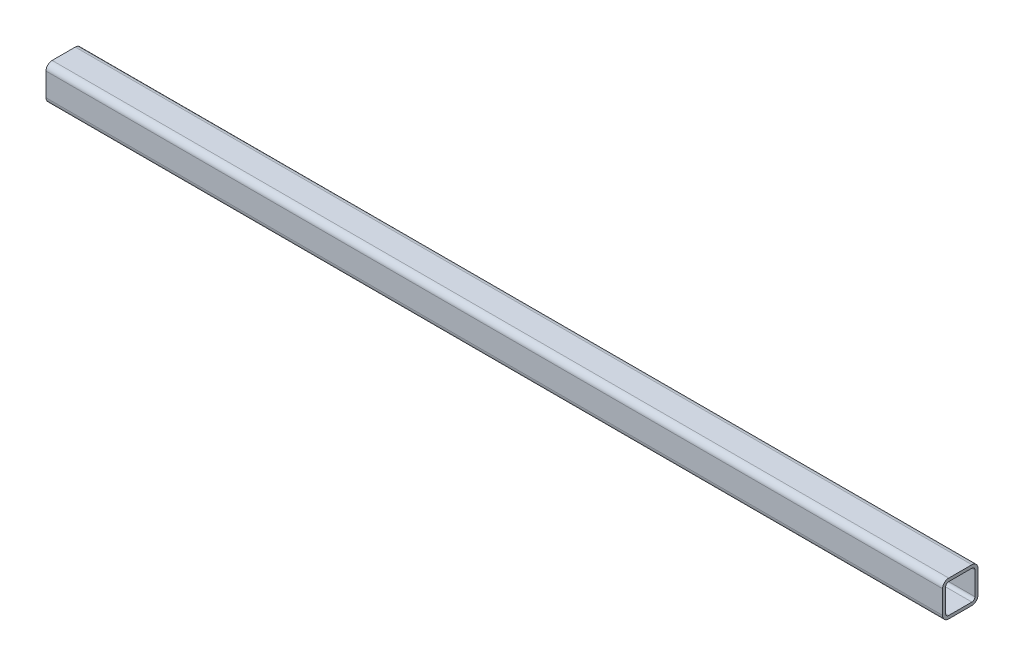
SolidWorks part; units mm, degrees
ref_plane "Front Plane" through (0, 0, 0) normal (0, 0, 1) x (1, 0, 0)
ref_plane "Top Plane" through (0, 0, 0) normal (0, 1, 0) x (1, 0, 0)
ref_plane "Right Plane" through (0, 0, 0) normal (1, 0, 0) x (0, 0, -1)
sketch "Sketch1" plane through (0, 0, 0) normal (0, 1, 0) x (1, 0, 0)
  line L0 (-380, 0) -> (380, 0)
  line L1 (0, 52.4254) -> (0, -55.906) construction
  dimension "D1" = 760
other "Square tube - configured 30 X 30 X 2.6(1)"
ref_plane "Plane1" through (-380, 0, 0) normal (1, 0, 0) x (0, 1, 0)
sketch "Sketch13" plane through (-380, 0, 0) normal (1, 0, 0) x (0, 1, 0)
  line L0 (-9.8, -12.4) -> (9.8, -12.4)
  line L1 (-12.4, -9.8) -> (-12.4, 9.8)
  line L2 (9.8, 12.4) -> (-9.8, 12.4)
  line L3 (12.4, 9.8) -> (12.4, -9.8)
  line L4 (-9.8, -15) -> (9.8, -15)
  line L5 (-15, -9.8) -> (-15, 9.8)
  line L6 (9.8, 15) -> (-9.8, 15)
  line L7 (15, 9.8) -> (15, -9.8)
  arc A0 (15, 9.8) -> (9.8, 15) centre (9.8, 9.8) ccw
  arc A1 (9.8, -15) -> (15, -9.8) centre (9.8, -9.8) ccw
  arc A2 (-15, -9.8) -> (-9.8, -15) centre (-9.8, -9.8) ccw
  arc A3 (-9.8, 15) -> (-15, 9.8) centre (-9.8, 9.8) ccw
  arc A4 (-9.8, 12.4) -> (-12.4, 9.8) centre (-9.8, 9.8) ccw
  arc A5 (12.4, 9.8) -> (9.8, 12.4) centre (9.8, 9.8) ccw
  arc A6 (9.8, -12.4) -> (12.4, -9.8) centre (9.8, -9.8) ccw
  arc A7 (-12.4, -9.8) -> (-9.8, -12.4) centre (-9.8, -9.8) ccw
  point P0 (-15, 0)
  point P1 (15, 0)
  point P2 (0, 15)
  point P3 (0, -15)
  point P4 (0, 0)
  point P5 (-15, -15)
  point P6 (15, -15)
  point P7 (15, 15)
  point P8 (-15, 15)
  point P33 (0, 0)
  dimension "D1" = 5.2
  dimension "Thickness" = 2.6
  dimension "V_leg" = 30
